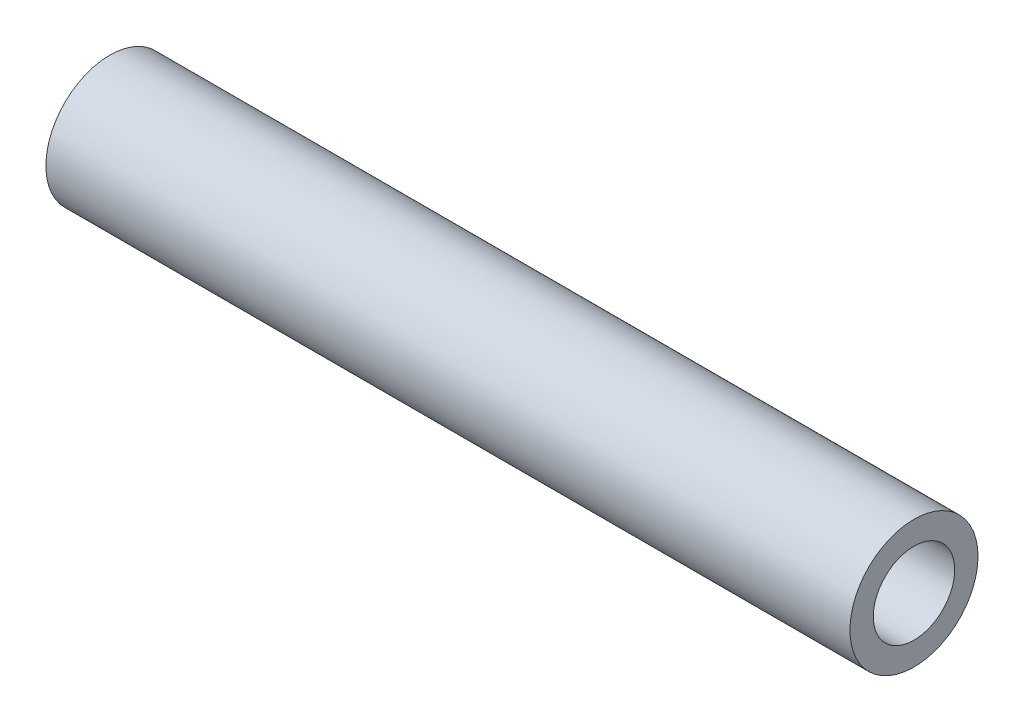
SolidWorks part; units mm, degrees
material "6061-T6 (SS)"
ref_plane "Front" through (0, 0, 0) normal (0, 0, 1) x (1, 0, 0)
ref_plane "Top" through (0, 0, 0) normal (0, 1, 0) x (1, 0, 0)
ref_plane "Right" through (0, 0, 0) normal (1, 0, 0) x (0, 0, -1)
sketch "Sketch1" plane through (0, 0, 0) normal (1, 0, 0) x (0, 0, -1)
  circle A0 centre (0, 0) radius 1.9304
  circle A1 centre (0, 0) radius 3.175
  dimension "D1" = 1.2446
  dimension "D2" = 6.35
extrude "Boss-Extrude1" add sketch "Sketch1" along normal mid plane 39.878
sketch "Sketch4" plane through (19.939, 0, 0) normal (1, 0, 0) x (0, 0, -1)
  point P0 (0, 0)
hole_wizard "#10-32 Tapped Hole1" positions "Sketch4" profile "Sketch3" tap size "#10-32" standard "ANSI Inch" end condition through all
sketch "Sketch3" plane through (19.939, 0, 0) normal (0, 1, 0) x (0, 0, -1)
  line L0 (0, 0) -> (0, 39.878)
  line L1 (0, 39.878) -> (2.0193, 39.878)
  line L2 (2.0193, 39.878) -> (2.0193, 0)
  line L5 (2.0193, 0) -> (0, 0)
  line L11 (0, -6.35) -> (0, 107.95) construction
  dimension "Thru Tap Drill Dia." = 4.0386
  dimension "Thru Tap Drill Depth" = 39.878
cosmetic thread "Hole Thread1"
